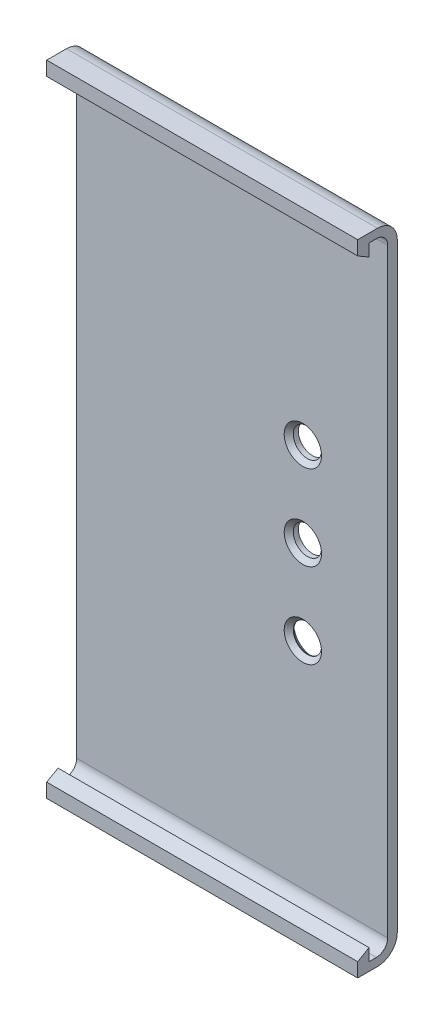
SolidWorks part; units mm, degrees
ref_plane "Front Plane" through (0, 0, 0) normal (0, 0, 1) x (1, 0, 0)
ref_plane "Top Plane" through (0, 0, 0) normal (0, 1, 0) x (1, 0, 0)
ref_plane "Right Plane" through (0, 0, 0) normal (1, 0, 0) x (0, 0, -1)
sketch "Sketch1" plane through (0, 0, 0) normal (1, 0, 0) x (0, 0, -1)
  line L0 (-69.7492, 110.9032) -> (-69.7492, 113.0579)
  line L1 (-69.7492, 112.3032) -> (-69.7492, 110.3032) construction
  line L2 (-69.7492, 113.0579) -> (-68.4492, 113.0579)
  line L3 (-66.4492, 111.0579) -> (-66.4492, 4.9737)
  line L6 (-69.7492, 5.7284) -> (-69.7492, 3.7284) construction
  line L8 (-71.7492, 3.9737) -> (-71.7492, 1.4737)
  line L9 (-71.7492, 1.4737) -> (-68.2492, 1.4737)
  line L10 (-64.7492, 4.9737) -> (-64.7492, 111.0579)
  line L11 (-68.2492, 114.5579) -> (-71.7492, 114.5579)
  line L12 (-71.7492, 114.5579) -> (-71.7492, 112.0579)
  line L14 (-66.7492, 104.0159) -> (-66.7492, 110.3032) construction
  line L15 (-69.7492, 110.9032) -> (-71.7492, 112.0579)
  line L17 (-83.7492, 110.3032) -> (-66.7492, 110.3032) construction
  line L18 (-69.7492, 5.1284) -> (-71.7492, 3.9737)
  line L21 (-83.7492, 5.7284) -> (-66.7492, 5.7284) construction
  line L22 (-69.7492, 5.1284) -> (-69.7492, 2.9737)
  line L23 (-69.7492, 2.9737) -> (-68.4492, 2.9737)
  arc A0 (-66.4492, 111.0579) -> (-68.4492, 113.0579) centre (-68.4492, 111.0579) ccw
  arc A1 (-68.2492, 114.5579) -> (-64.7492, 111.0579) centre (-68.2492, 111.0579) cw
  arc A2 (-66.4492, 4.9737) -> (-68.4492, 2.9737) centre (-68.4492, 4.9737) cw
  arc A3 (-64.7492, 4.9737) -> (-68.2492, 1.4737) centre (-68.2492, 4.9737) cw
  point P18 (-69.7492, 111.9805)
  point P24 (-64.7492, 114.5579)
  dimension "D8" = 2
  dimension "D9" = 3.5
  dimension "D13" = 2
  dimension "D14" = 3.5
  dimension "D1" = 2.5
  dimension "D2" = 60
  dimension "D3" = 1.5
  dimension "D4" = 0.3
  dimension "D5" = 2
  dimension "D6" = 60
  dimension "D7" = 2.5
  dimension "D10" = 0.6
  dimension "D11" = 1.5
  dimension "D12" = 0.6
extrude "Boss-Extrude1" add sketch "Sketch1" along normal blind 55
sketch "Sketch2" plane through (0, 0, 66.4492) normal (0, 0, 1) x (1, 0, 0)
  line L0 (55, 1.4737) -> (0, 1.4737) construction
  line L2 (55, 111.0579) -> (55, 4.9737) construction
  circle A0 centre (40, 72.9737) radius 2.5
  circle A1 centre (40, 57.9737) radius 2.5
  circle A2 centre (40, 42.9737) radius 2.5
  dimension "D1" = 5
  dimension "D2" = 5
  dimension "D3" = 5
  dimension "D4" = 56.5
  dimension "D5" = 15
  dimension "D6" = 15
  dimension "D7" = 15
extrude "Cut-Extrude1" cut sketch "Sketch2" against normal up to next
chamfer "Chamfer1" distance 0.8 angle 45 4 edges at (40, 40.4737, 64.7492) (42.5, 42.9737, 66.4492) (42.5, 57.9737, 66.4492) (42.5, 72.9737, 66.4492)
